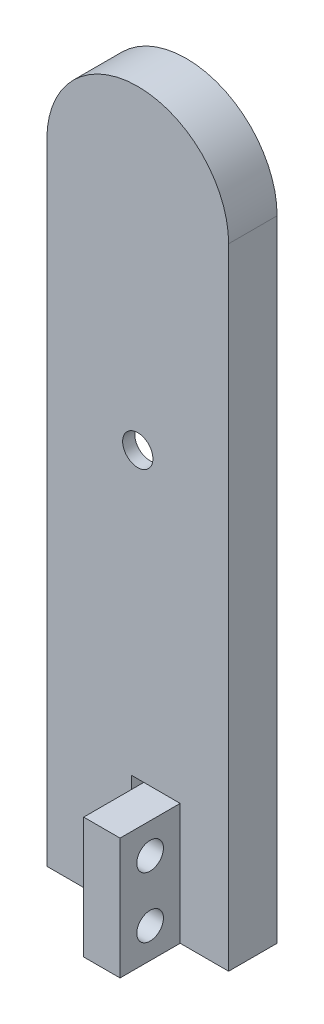
SolidWorks part; units mm, degrees
ref_plane "前基準面" through (0, 0, 0) normal (0, 0, 1) x (1, 0, 0)
ref_plane "上基準面" through (0, 0, 0) normal (0, 1, 0) x (1, 0, 0)
ref_plane "右基準面" through (0, 0, 0) normal (1, 0, 0) x (0, 0, -1)
sketch "草圖1" plane through (0, 0, 0) normal (0, 0, 1) x (1, 0, 0)
  line L0 (0, 0) -> (0, 4.6483) construction
  line L1 (7.5, 0) -> (7.5, 52)
  line L2 (7.5, 0) -> (-7.5, 0)
  line L3 (-7.5, 0) -> (-7.5, 52)
  arc A0 (7.5, 52) -> (-7.5, 52) centre (0, 52) ccw
  dimension "D1" = 7.5
  dimension "D2" = 52
extrude "填料-伸長1" add sketch "草圖1" along normal blind 4
sketch "草圖3" plane through (0, 0, 0) normal (0, 0, 1) x (1, 0, 0)
  line L0 (0, 0) -> (0, 14.6981) construction
  line L1 (7.5, 52) -> (-7.5, 52) construction
  line L2 (7.5, 15) -> (-7.5, 15) construction
  line L3 (7.5, 0) -> (7.5, 52) construction
  line L4 (-7.5, 52) -> (-7.5, 0) construction
  line L5 (-7.5, 0) -> (7.5, 0) construction
  line L6 (7.5, 33.5) -> (5, 33.5) construction
  line L7 (5, 33.5) -> (2.2723, 16.6325)
  line L8 (5, 33.5) -> (2.2966, 50)
  line L9 (-2.2966, 50) -> (-5, 33.5)
  line L10 (-5, 33.5) -> (-2.3019, 17)
  line L11 (0, 52.2966) -> (0, 59.5) construction
  line L12 (-5, 33.5) -> (-7.5, 33.5) construction
  arc A0 (7.5, 52) -> (-7.5, 52) centre (0, 52) ccw construction
  arc A1 (-4.7386, 35.0956) -> (-4.7396, 31.9073) centre (0, 33.5) ccw
  arc A2 (-2.3019, 17) -> (2.2723, 16.6325) centre (0, 17) ccw
  arc A3 (-2.2966, 50) -> (2.2966, 50) centre (0, 50) cw
  arc A4 (4.7452, 31.9241) -> (4.7386, 35.0956) centre (0, 33.5) ccw
  dimension "D4" = 10
  dimension "D5" = 16.5
  dimension "D1" = 15
  dimension "D2" = 37
  dimension "D3" = 18.5
extrude "除料-伸長1" cut sketch "草圖3" along normal blind 3 contours A3 L9 L10 A2 L7 L8
sketch "草圖5" plane through (0, 0, 0) normal (0, 0, 1) x (1, 0, 0)
  line L0 (5, 33.5) -> (-5, 33.5) construction
  circle A0 centre (0, 33.5) radius 1.25
  dimension "D1" = 2.5
extrude "除料-伸長2" cut sketch "草圖5" along normal blind 12.4
sketch "草圖6" plane through (0, 0, 0) normal (0, 0, 1) x (1, 0, 0)
  line L0 (0, 0) -> (0, 56.6939) construction
  line L1 (0.5, 0) -> (0.5, 10)
  line L2 (7.5, 0) -> (-7.5, 0) construction
  line L3 (0.5, 10) -> (-0.5, 10)
  line L4 (0.5, 0) -> (-0.5, 0)
  line L5 (-0.5, 0) -> (-0.5, 10)
  point P10 (0, 10)
  dimension "D1" = 0.5
  dimension "D2" = 10
extrude "除料-伸長3" cut sketch "草圖6" along normal blind 16.3
ref_plane "平面1" through (0.5, 0, 0) normal (1, 0, 0) x (0, 0, -1)
sketch "草圖9" plane through (0.5, 0, 0) normal (1, 0, 0) x (0, 0, -1)
  line L0 (-4, 0) -> (0, 0) construction
  line L1 (-8.9618, 10) -> (-3.9618, 10)
  line L2 (-8.9618, 10) -> (-8.9618, 0)
  line L3 (-8.9618, 0) -> (-3.9618, 0)
  line L4 (-3.9618, 10) -> (-3.9618, 0)
  dimension "D1" = 5
  dimension "D2" = 10
extrude "填料-伸長4" add sketch "草圖9" along normal blind 3
sketch "草圖10" plane through (0.5, 0, 0) normal (1, 0, 0) x (0, 0, -1)
  line L0 (-8.9618, 5) -> (-4, 5) construction
  line L1 (-8.9618, 10) -> (-8.9618, 0) construction
  line L2 (-4, 0) -> (-4, 10) construction
  line L3 (-6.4809, 10) -> (-6.4809, 0) construction
  line L4 (-4, 10) -> (-8.9618, 10) construction
  line L5 (-8.9618, 0) -> (-4, 0) construction
  circle A0 centre (-6.4809, 7.5) radius 1.1
  circle A1 centre (-6.4809, 2.5) radius 1.1
  dimension "D2" = 2.2
  dimension "D1" = 2.5
extrude "除料-伸長4" cut sketch "草圖10" along normal blind 5.1
